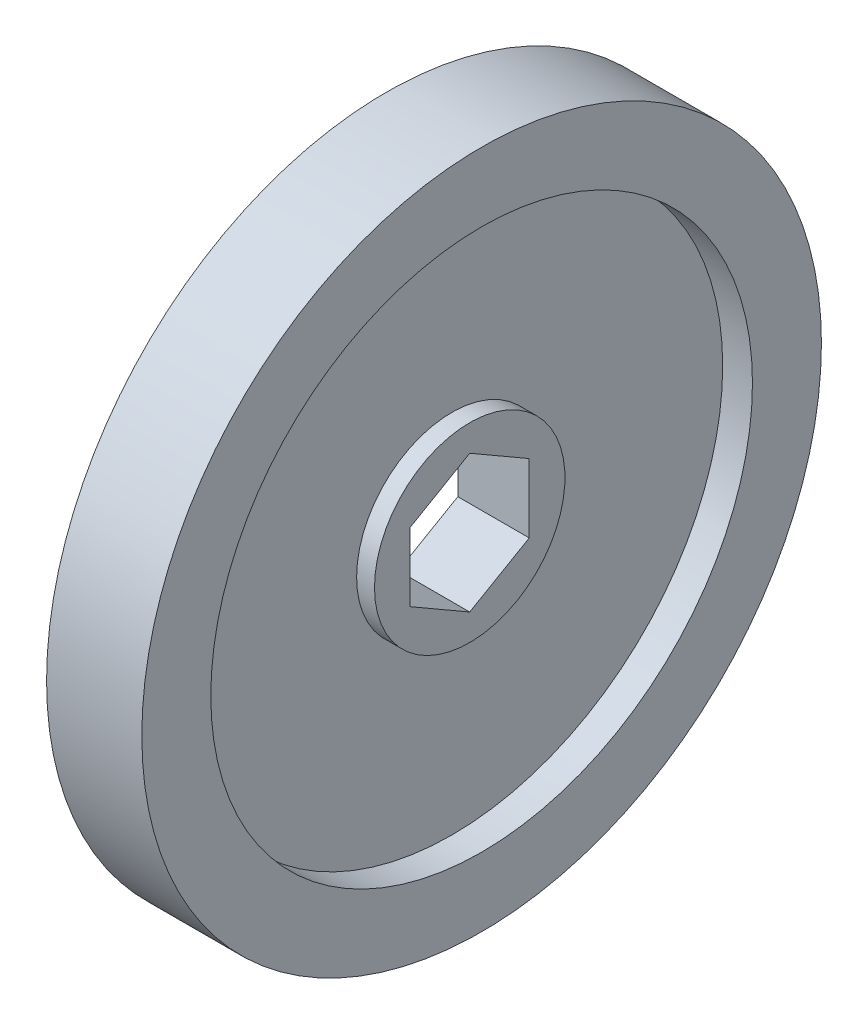
SolidWorks part; units mm, degrees
ref_plane "Plan de face" through (0, 0, 0) normal (0, 0, 1) x (1, 0, 0)
ref_plane "Plan de dessus" through (0, 0, 0) normal (0, 1, 0) x (1, 0, 0)
ref_plane "Plan de droite" through (0, 0, 0) normal (1, 0, 0) x (0, 0, -1)
sketch "Esquisse1" plane through (0, 0, 0) normal (0, 0, 1) x (1, 0, 0)
  line L0 (-12.566, 0) -> (17.5241, 0) construction
  line L1 (-5.08, 36.25) -> (5.08, 36.25)
  line L2 (5.08, 36.25) -> (5.08, 28.8925)
  line L3 (5.08, 28.8925) -> (1.905, 28.8925)
  line L4 (1.905, 28.8925) -> (1.905, 10.16)
  line L5 (1.905, 10.16) -> (3.81, 10.16)
  line L6 (3.81, 10.16) -> (3.81, 0)
  line L7 (3.81, 0) -> (-3.81, 0)
  line L8 (0, 0) -> (0, 49.4244) construction
  line L9 (-3.81, 10.16) -> (-3.81, 0)
  line L10 (-1.905, 10.16) -> (-3.81, 10.16)
  line L11 (-1.905, 28.8925) -> (-1.905, 10.16)
  line L12 (-5.08, 28.8925) -> (-1.905, 28.8925)
  line L13 (-5.08, 36.25) -> (-5.08, 28.8925)
  point P18 (0, 36.25)
  dimension "D1" = 10.16
  dimension "D2" = 7.62
  dimension "D3" = 3.81
  dimension "D4" = 72.5
  dimension "D5" = 20.32
  dimension "D6" = 57.785
revolve "Révolution1" add sketch "Esquisse1" angle 360 about L0
sketch "Esquisse2" plane through (3.81, 0, 0) normal (1, 0, 0) x (0, 0, -1)
  line L1 (0, 7.3323) -> (-6.35, 3.6662)
  line L2 (-6.35, 3.6662) -> (-6.35, -3.6662)
  line L3 (-6.35, -3.6662) -> (0, -7.3323)
  line L4 (0, -7.3323) -> (6.35, -3.6662)
  line L5 (6.35, -3.6662) -> (6.35, 3.6662)
  line L6 (6.35, 3.6662) -> (0, 7.3323)
  circle A0 centre (0, 0) radius 6.35 construction
  dimension "D1" = 12.7
extrude "Enlèv. mat.-Extru.1" cut sketch "Esquisse2" against normal through all
